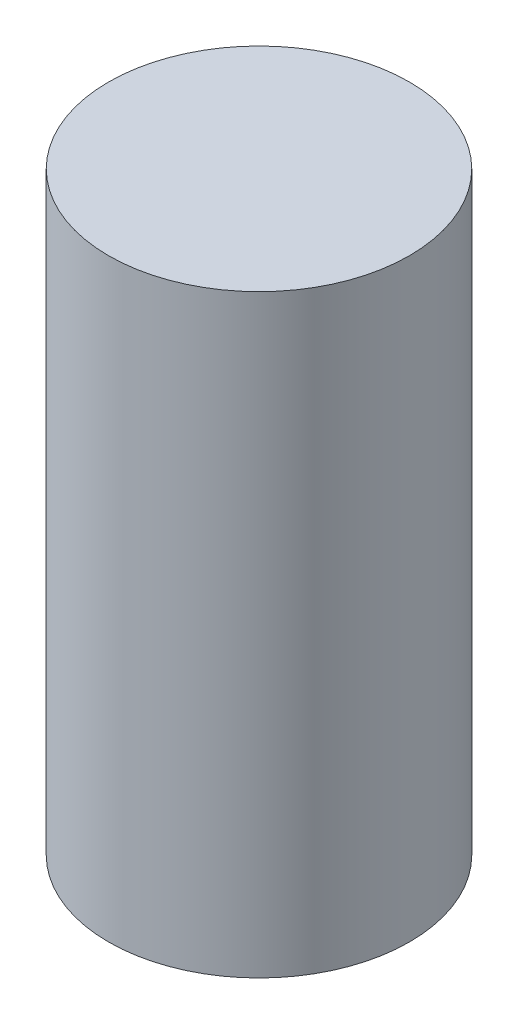
SolidWorks part; units mm, degrees
ref_plane "Front Plane" through (0, 0, 0) normal (0, 0, 1) x (1, 0, 0)
ref_plane "Top Plane" through (0, 0, 0) normal (0, 1, 0) x (1, 0, 0)
ref_plane "Right Plane" through (0, 0, 0) normal (1, 0, 0) x (0, 0, -1)
sketch "Sketch1" plane through (0, 0, 0) normal (0, 1, 0) x (1, 0, 0)
  line L1 (9.3567, 0.7937) -> (5.3657, 7.7063)
  line L2 (3.9909, 8.5) -> (-3.9909, 8.5)
  line L3 (-5.3657, 7.7063) -> (-9.3567, 0.7938)
  line L4 (-9.3567, -0.7937) -> (-5.3657, -7.7063)
  line L5 (-3.9909, -8.5) -> (3.9909, -8.5)
  line L6 (5.3657, -7.7063) -> (9.3567, -0.7938)
  circle A0 centre (0, 0) radius 8.5 construction
  circle A1 centre (0, 0) radius 10.125
  arc A8 (-3.9909, 8.5) -> (-5.3657, 7.7063) centre (-3.9909, 6.9125) ccw
  arc A9 (5.3657, 7.7063) -> (3.9909, 8.5) centre (3.9909, 6.9125) ccw
  arc A10 (9.3567, -0.7938) -> (9.3567, 0.7937) centre (7.9819, 0) ccw
  arc A11 (3.9909, -8.5) -> (5.3657, -7.7063) centre (3.9909, -6.9125) ccw
  arc A13 (-9.3567, 0.7938) -> (-9.3567, -0.7937) centre (-7.9819, 0) ccw
  arc A14 (-5.3657, -7.7063) -> (-3.9909, -8.5) centre (-3.9909, -6.9125) ccw
  point P5 (-3.3531, -8.5)
  point P22 (-3.5954, -6.2274)
  dimension "D1" = 20.25
  dimension "D3" = 3.175
  dimension "D2" = 17
extrude "Boss-Extrude1" add sketch "Sketch1" along normal blind 10
sketch "Sketch2" plane through (0, 10, 0) normal (0, 1, 0) x (1, 0, 0)
  circle A0 centre (0, 0) radius 10.125 construction
  circle A1 centre (0, 0) radius 10.125
extrude "Boss-Extrude2" add sketch "Sketch2" along normal blind 30
